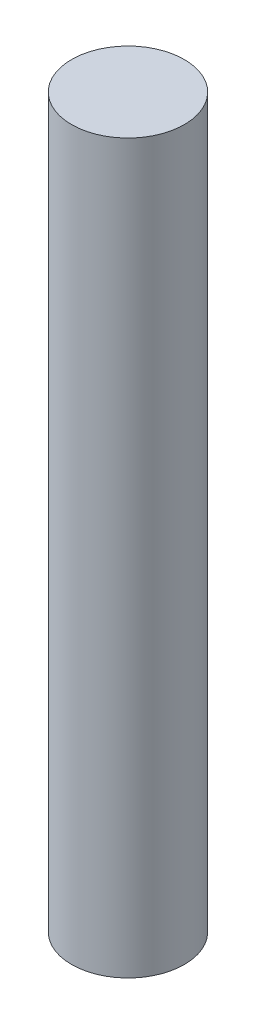
SolidWorks part; units mm, degrees
ref_plane "正面" through (0, 0, 0) normal (0, 0, 1) x (1, 0, 0)
ref_plane "平面" through (0, 0, 0) normal (0, 1, 0) x (1, 0, 0)
ref_plane "右側面" through (0, 0, 0) normal (1, 0, 0) x (0, 0, -1)
sketch "ｽｹｯﾁ1" plane through (0, 0, 0) normal (0, 1, 0) x (1, 0, 0)
  circle A0 centre (0, 0) radius 4
  dimension "D1" = 8
extrude "ﾎﾞｽ - 押し出し1" add sketch "ｽｹｯﾁ1" along normal blind 51.6
